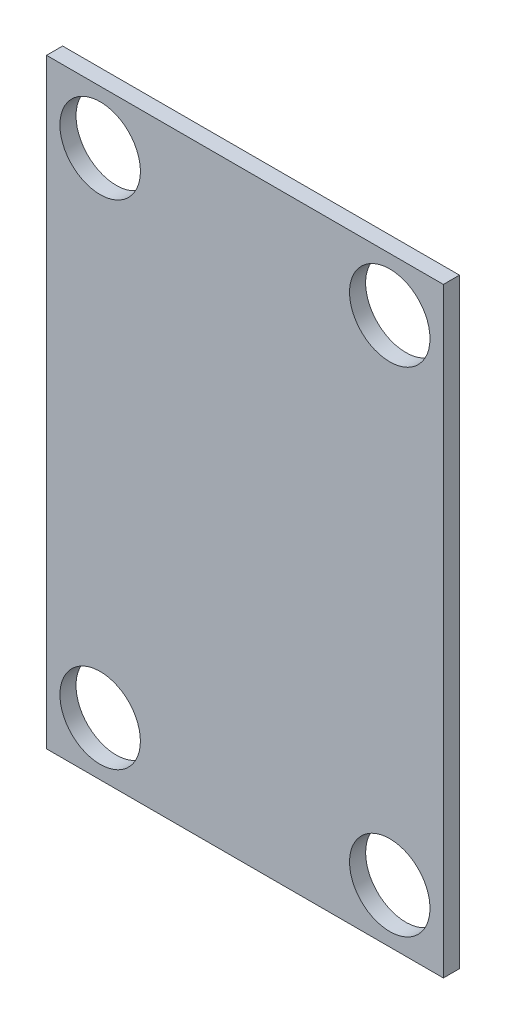
SolidWorks part; units mm, degrees
ref_plane "Спереди" through (0, 0, 0) normal (0, 0, 1) x (1, 0, 0)
ref_plane "Сверху" through (0, 0, 0) normal (0, 1, 0) x (1, 0, 0)
ref_plane "Справа" through (0, 0, 0) normal (1, 0, 0) x (0, 0, -1)
sketch "Эскиз3" plane through (0, 0, 0) normal (0, 0, 1) x (1, 0, 0)
  line L4 (-0.5405, 29.5) -> (-0.5405, -29.5) construction
  line L5 (19.4595, 0) -> (-20.5405, 0) construction
  line L7 (17.9595, 28) -> (-19.0405, 28)
  line L8 (17.9595, 28) -> (17.9595, -28)
  line L9 (17.9595, -28) -> (-19.0405, -28)
  line L10 (-19.0405, 28) -> (-19.0405, -28)
  circle A0 centre (-14.0405, 23) radius 3.75
  circle A1 centre (-14.0405, -23) radius 3.75
  circle A2 centre (12.9595, 23) radius 3.75
  circle A3 centre (12.9595, -23) radius 3.75
  dimension "D1" = 7.5
extrude "Бобышка-Вытянуть1" add sketch "Эскиз3" along normal blind 1.5
